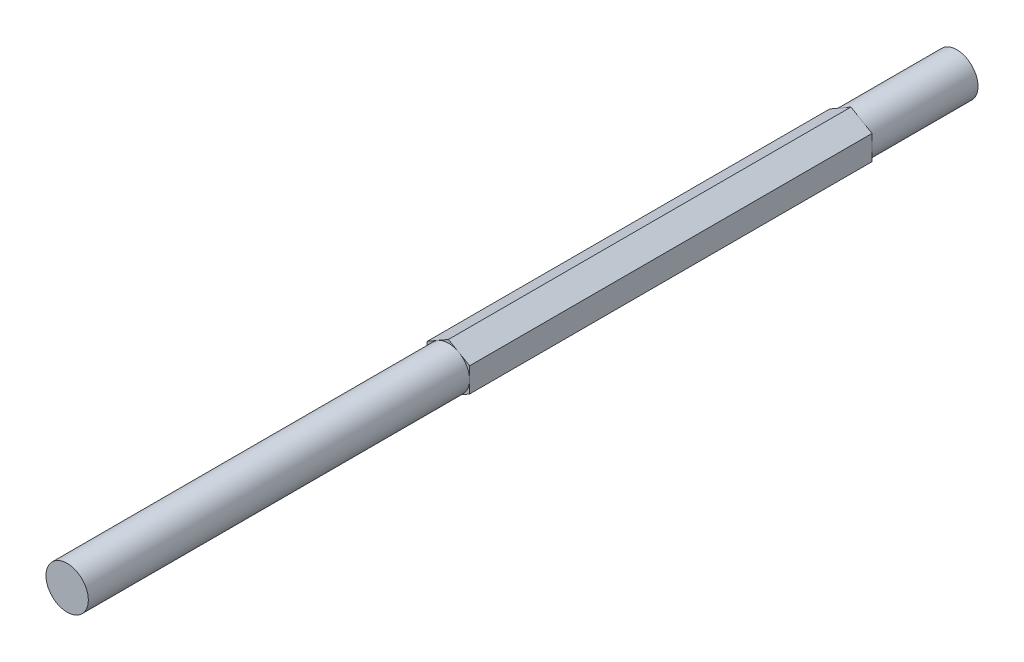
SolidWorks part; units mm, degrees
ref_plane "Front Plane" through (0, 0, 0) normal (0, 0, 1) x (1, 0, 0)
ref_plane "Top Plane" through (0, 0, 0) normal (0, 1, 0) x (1, 0, 0)
ref_plane "Right Plane" through (0, 0, 0) normal (1, 0, 0) x (0, 0, -1)
sketch "Sketch2" plane through (0, 0, 0) normal (0, 0, 1) x (1, 0, 0)
  line L1 (0, 3.6662) -> (-3.175, 1.8331)
  line L2 (-3.175, 1.8331) -> (-3.175, -1.8331)
  line L3 (-3.175, -1.8331) -> (0, -3.6662)
  line L4 (0, -3.6662) -> (3.175, -1.8331)
  line L5 (3.175, -1.8331) -> (3.175, 1.8331)
  line L6 (3.175, 1.8331) -> (0, 3.6662)
  circle A0 centre (0, 0) radius 3.175 construction
  dimension "D1" = 6.35
extrude "Boss-Extrude1" add sketch "Sketch2" along normal blind 133.35
sketch "Sketch3" plane through (0, 0, 133.35) normal (0, 0, 1) x (1, 0, 0)
  circle A0 centre (0, 0) radius 3.175
  dimension "D1" = 6.35
extrude "Cut-Extrude1" cut sketch "Sketch3" against normal blind 57.15 flip side to cut
sketch "Sketch4" plane through (0, 0, 0) normal (0, 0, -1) x (-1, 0, 0)
  line L0 (0, 3.6662) -> (3.175, 1.8331) construction
  circle A0 centre (0, 0) radius 3.175
  point P5 (1.5875, 2.7496)
extrude "Cut-Extrude2" cut sketch "Sketch4" against normal blind 15.875 flip side to cut
